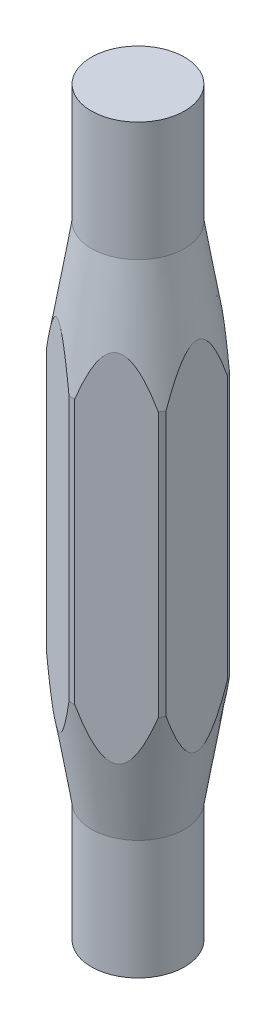
SolidWorks part; units mm, degrees
material "6061-T6 (SS)"
ref_plane "Front Plane" through (0, 0, 0) normal (0, 0, 1) x (1, 0, 0)
ref_plane "Top Plane" through (0, 0, 0) normal (0, 1, 0) x (1, 0, 0)
ref_plane "Right Plane" through (0, 0, 0) normal (1, 0, 0) x (0, 0, -1)
sketch "Sketch1" plane through (0, 0, 0) normal (0, 0, 1) x (1, 0, 0)
  line L0 (2.2371, -12.065) -> (3.175, -6.35)
  line L1 (3.175, -6.35) -> (3.175, 6.35)
  line L2 (3.175, 6.35) -> (2.2371, 12.065)
  line L3 (2.2371, 12.065) -> (2.2371, -12.065)
  line L4 (2.2371, 0) -> (3.175, 0) construction
  line L5 (0, 6.0414) -> (0, -4.6122) construction
  dimension "D1" = 24.13
  dimension "D2" = 12.7
  dimension "D3" = 3.175
revolve "Revolve1" add sketch "Sketch1" angle 360 about L5
ref_plane "Plane1" through (0, 0, 3.175) normal (0, 0, 1) x (1, 0, 0)
sketch "Sketch3" plane through (0, 0, 3.175) normal (0, 0, 1) x (1, 0, 0)
  line L1 (-3.2443, -10.1093) -> (-2.8155, -10.1093)
  line L2 (-3.2443, -10.1093) -> (-3.2443, 8.7912)
  line L3 (-3.2443, 8.7912) -> (-2.8155, 8.7912)
  line L4 (-2.8155, -10.1093) -> (-2.8155, 8.7912)
extrude "Cut-Extrude1" cut sketch "Sketch3" against normal through all
pattern_circular "CirPattern1" count 6 over 360 about axis through (0, 0, 0) along (0, 1, 0) of "Cut-Extrude1"
sketch "Sketch5" plane through (0, 0, 0) normal (0, 1, 0) x (1, 0, 0)
  circle A0 centre (0, 0) radius 2.2371
  circle A1 centre (0, 0) radius 2.2371 construction
extrude "Boss-Extrude1" add sketch "Sketch5" along normal blind 17.78 and the other way blind 17.78
